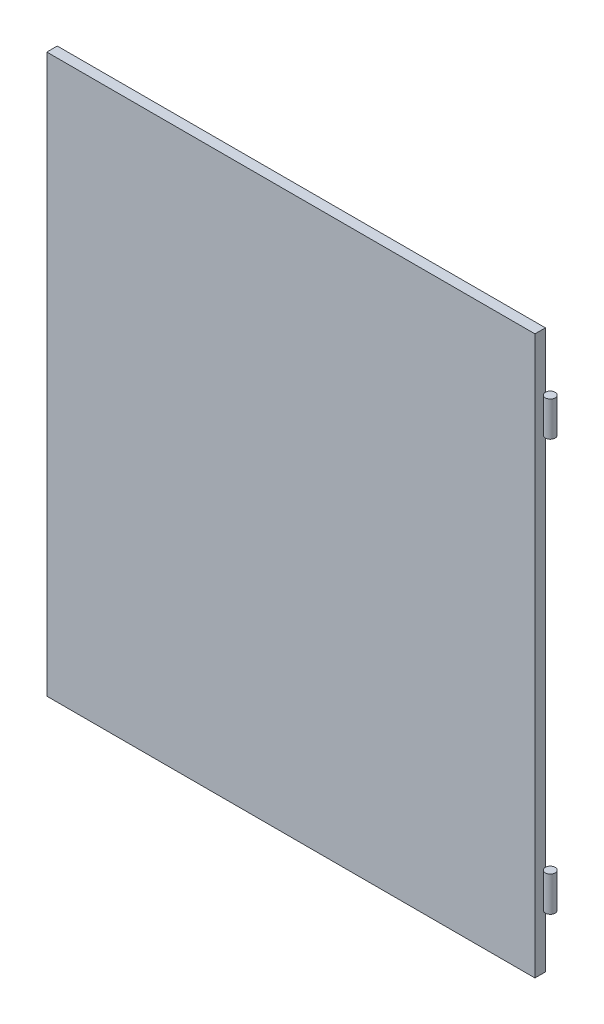
SolidWorks part; units mm, degrees
ref_plane "Alzado" through (0, 0, 0) normal (0, 0, 1) x (1, 0, 0)
ref_plane "Planta" through (0, 0, 0) normal (0, 1, 0) x (1, 0, 0)
ref_plane "Vista lateral" through (0, 0, 0) normal (1, 0, 0) x (0, 0, -1)
sketch "Croquis1" plane through (0, 0, 0) normal (0, 0, 1) x (1, 0, 0)
  line L1 (0, 0) -> (700, 0)
  line L2 (0, 0) -> (0, -800)
  line L3 (0, -800) -> (700, -800)
  line L4 (700, 0) -> (700, -800)
  dimension "D1" = 800
  dimension "D2" = 700
extrude "Saliente-Extruir1" add sketch "Croquis1" along normal blind 15
sketch "Croquis2" plane through (0, 0, 0) normal (0, 0, -1) x (-1, 0, 0)
  line L8 (-5, -795) -> (-5, -5)
  line L9 (-5, -5) -> (-695, -5)
  line L10 (-695, -5) -> (-695, -795)
  line L11 (-695, -795) -> (-5, -795)
  line L12 (-5, -795) -> (-5, -5)
  line L13 (-5, -5) -> (-695, -5)
  line L14 (-695, -5) -> (-695, -795)
  line L15 (-695, -795) -> (-5, -795)
  dimension "D1" = 5
extrude "Cortar-Extruir1" cut sketch "Croquis2" against normal blind 10
sketch "Croquis4" plane through (0, 0, 0) normal (0, 1, 0) x (1, 0, 0)
  line L0 (700, 0) -> (707, 0) construction
  circle A0 centre (707, 0) radius 7
  dimension "D1" = 7
extrude "Saliente-Extruir2" add sketch "Croquis4" against normal up to surface (800 mm away) separate body up to face at (350, -800, 7.5)
sketch "Croquis5" plane through (0, 0, 15) normal (0, 0, 1) x (1, 0, 0)
  line L0 (700, -400) -> (752.3349, -400) construction
  line L1 (700, 0) -> (752.3349, 0)
  line L2 (700, 0) -> (700, -80)
  line L3 (700, -80) -> (752.3349, -80)
  line L4 (752.3349, 0) -> (752.3349, -80)
  line L5 (700, -800) -> (752.3349, -800)
  line L6 (700, -800) -> (700, -720)
  line L7 (700, -720) -> (752.3349, -720)
  line L8 (752.3349, -800) -> (752.3349, -720)
  line L9 (700, 0) -> (700, -800) construction
  line L11 (700, -670) -> (752.3349, -670)
  line L12 (700, -670) -> (700, -130)
  line L13 (700, -130) -> (752.3349, -130)
  line L14 (752.3349, -670) -> (752.3349, -130)
  line L15 (700, -670) -> (752.3349, -130) construction
  line L16 (700, -130) -> (752.3349, -670) construction
  point P14 (726.1675, -400)
  dimension "D1" = 80
  dimension "D2" = 80
  dimension "D3" = 540
extrude "Cortar-Extruir2" cut sketch "Croquis5" against normal blind 25
